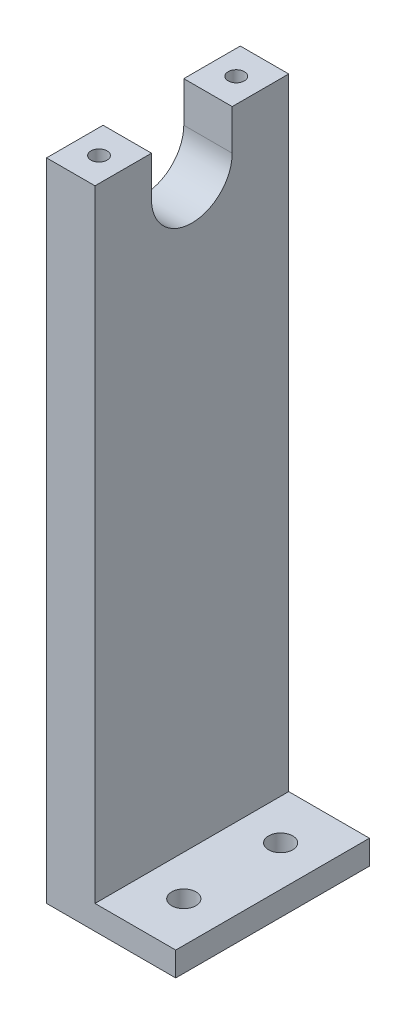
SolidWorks part; units mm, degrees
material "1060 Alloy"
ref_plane "Front" through (0, 0, 0) normal (0, 0, 1) x (1, 0, 0)
ref_plane "Top" through (0, 0, 0) normal (0, 1, 0) x (1, 0, 0)
ref_plane "Right" through (0, 0, 0) normal (1, 0, 0) x (0, 0, -1)
sketch "Sketch1" plane through (0, 0, 0) normal (0, 1, 0) x (1, 0, 0)
  line L1 (-1.5, -6) -> (1.5, -6)
  line L2 (-1.5, -6) -> (-1.5, 6)
  line L3 (-1.5, 6) -> (1.5, 6)
  line L4 (1.5, -6) -> (1.5, 6)
  line L5 (-1.5, -6) -> (1.5, 6) construction
  line L6 (-1.5, 6) -> (1.5, -6) construction
  point P0 (0, 0)
  dimension "D1" = 3
  dimension "D2" = 12
extrude "Boss-Extrude1" add sketch "Sketch1" along normal blind 40
sketch "Sketch2" plane through (1.5, 0, 0) normal (1, 0, 0) x (0, 0, -1)
  line L0 (-2.5, 40) -> (-2.5, 37.5)
  line L1 (-2.5, 40) -> (2.5, 40)
  line L2 (2.5, 40) -> (2.5, 37.5)
  line L3 (-6, 40) -> (6, 40) construction
  line L4 (0, 1.65) -> (0, -1.65) construction
  arc A0 (2.5, 37.5) -> (-2.5, 37.5) centre (0, 37.5) cw
  dimension "D7" = 2.5
  dimension "D1" = 2.5
  dimension "D2" = 0
  dimension "D3" = 2.5
  dimension "D4" = 0
  dimension "D5" = 2.5
  dimension "D6" = 2.5
extrude "Cut-Extrude1" cut sketch "Sketch2" against normal blind 3
sketch "Sketch3" plane through (0, 40, 0) normal (0, 1, 0) x (1, 0, 0)
  line L2 (-1.5, -6) -> (1.5, -6) construction
  line L3 (1.5, 6) -> (-1.5, 6) construction
  circle A0 centre (0, -4.25) radius 0.5
  circle A1 centre (0, 4.25) radius 0.5
  dimension "D3" = 1
  dimension "D4" = 1
  dimension "D1" = 1.75
  dimension "D2" = 1.75
extrude "Cut-Extrude2" cut sketch "Sketch3" against normal blind 5
sketch "Sketch4" plane through (1.5, 0, 0) normal (1, 0, 0) x (0, 0, -1)
  line L1 (-6, 0) -> (6, 0)
  line L2 (-6, 0) -> (-6, 1.5)
  line L3 (-6, 1.5) -> (6, 1.5)
  line L4 (6, 0) -> (6, 1.5)
  dimension "D1" = 1.5
extrude "Boss-Extrude2" add sketch "Sketch4" along normal blind 5
sketch "Sketch5" plane through (0, 1.5, 0) normal (0, 1, 0) x (1, 0, 0)
  line L1 (6.5, 6) -> (6.5, -6) construction
  line L2 (6.5, 6) -> (1.5, 6) construction
  line L3 (6.5, -6) -> (1.5, -6) construction
  circle A0 centre (4, 3) radius 0.75
  circle A1 centre (4, -3) radius 0.75
  dimension "D5" = 1.5
  dimension "D6" = 1.5
  dimension "D1" = 2.5
  dimension "D2" = 2.5
  dimension "D3" = 3
  dimension "D4" = 3
extrude "Cut-Extrude3" cut sketch "Sketch5" against normal blind 5
